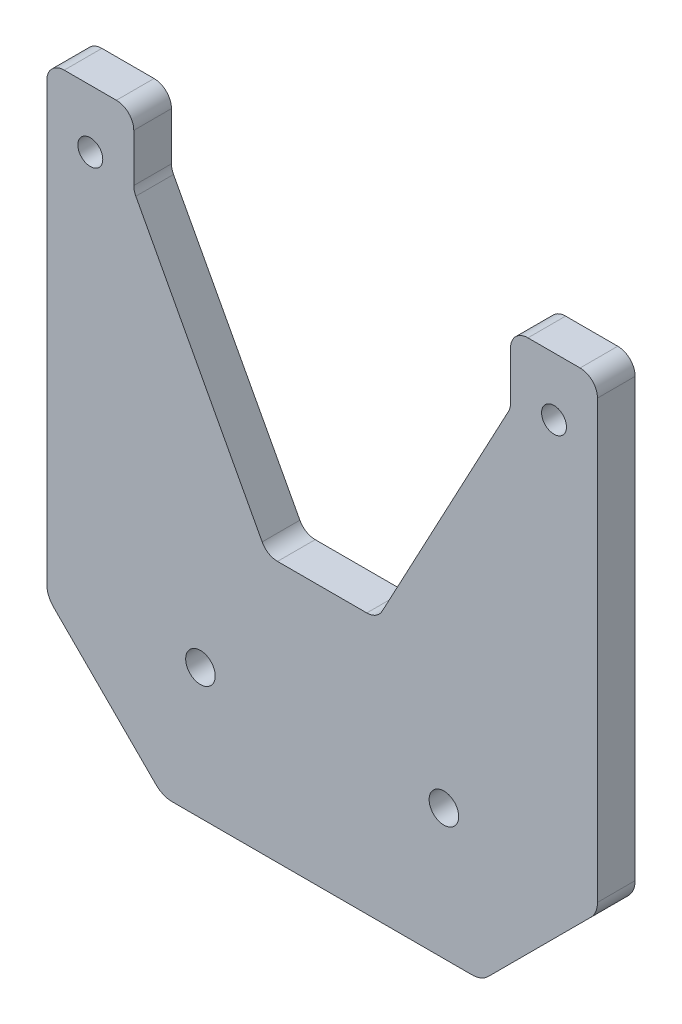
SolidWorks part; units mm, degrees
material "Balsa"
ref_plane "前视基准面" through (0, 0, 0) normal (0, 0, 1) x (1, 0, 0)
ref_plane "上视基准面" through (0, 0, 0) normal (0, 1, 0) x (1, 0, 0)
ref_plane "右视基准面" through (0, 0, 0) normal (1, 0, 0) x (0, 0, -1)
other "Configuration Table"
sketch "Sketch1" plane through (0, 0, 0) normal (0, 0, 1) x (1, 0, 0)
  line L0 (0, 56.7864) -> (0, -74.7826) construction
  line L1 (-32.5, 55) -> (-32.5, 0)
  line L2 (-32.5, 0) -> (32.5, 0)
  line L3 (-32.5, 55) -> (-47.5, 55)
  line L4 (-47.5, 55) -> (-47.5, -45)
  line L5 (-47.5, -45) -> (47.5, -45)
  line L6 (47.5, 55) -> (47.5, -45)
  line L7 (32.5, 55) -> (47.5, 55)
  line L8 (32.5, 55) -> (32.5, 0)
  line L9 (-32.5, 43) -> (-9.5, 0)
  line L10 (32.5, 43) -> (9.5, 0)
  circle A0 centre (-40, 45) radius 2.15
  circle A1 centre (40, 45) radius 2.15
  circle A2 centre (-21, -22.5) radius 2.55
  circle A3 centre (21, -22.5) radius 2.55
  point P10 (0, -45)
  point P13 (0, 0)
  point P20 (-40, 55)
  dimension "D7" = 4.3
  dimension "D9" = 5.1
  dimension "D10" = 42
  dimension "D1" = 80
  dimension "D2" = 100
  dimension "D3" = 15
  dimension "D4" = 45
  dimension "D5" = 23
  dimension "D6" = 43
  dimension "D8" = 10
  dimension "D11" = 22.5
extrude "Boss-Extrude1" add sketch "Sketch1" along normal blind 6.5 contours L0 L2 L1 L3 L4 L5 A0 A2 | L2 L0 L5 L6 L7 L8 A3 A1 | L9 L1 L2 | L8 L10 L2
fillet "Fillet1" radius 3 8 edges at (9.5, 0, 3.25) (32.5, 43, 3.25) (32.5, 55, 3.25) (47.5, 55, 3.25) (-32.5, 43, 3.25) (-9.5, 0, 3.25) (-47.5, 55, 3.25) (-32.5, 55, 3.25)
chamfer "Chamfer1" distance 20 angle 45 2 edges at (47.5, -45, 3.25) (-47.5, -45, 3.25)
fillet "Fillet2" radius 4 4 edges at (-27.5, -45, 3.25) (27.5, -45, 3.25) (47.5, -25, 3.25) (-47.5, -25, 3.25)
